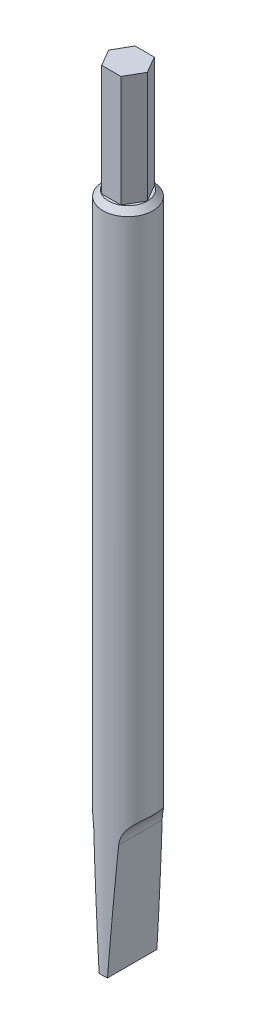
SolidWorks part; units mm, degrees
material "Cast Alloy Steel"
ref_plane "Front Plane" through (0, 0, 0) normal (0, 0, 1) x (1, 0, 0)
ref_plane "Top Plane" through (0, 0, 0) normal (0, 1, 0) x (1, 0, 0)
ref_plane "Right Plane" through (0, 0, 0) normal (1, 0, 0) x (0, 0, -1)
sketch "Sketch1" plane through (0, 0, 0) normal (0, 1, 0) x (1, 0, 0)
  circle A0 centre (0, 0) radius 4.5
  dimension "D1" = 9
extrude "Boss-Extrude1" add sketch "Sketch1" along normal blind 120
sketch "Sketch2" plane through (0, 120, 0) normal (0, 1, 0) x (1, 0, 0)
  line L1 (1.7321, 3) -> (-1.7321, 3)
  line L2 (-1.7321, 3) -> (-3.4641, 0)
  line L3 (-3.4641, 0) -> (-1.7321, -3)
  line L4 (-1.7321, -3) -> (1.7321, -3)
  line L5 (1.7321, -3) -> (3.4641, 0)
  line L6 (3.4641, 0) -> (1.7321, 3)
  circle A0 centre (0, 0) radius 3 construction
  dimension "D1" = 6
extrude "Boss-Extrude2" add sketch "Sketch2" along normal blind 20
chamfer "Chamfer1" distance 1 angle 45 1 edges at (0, 120, 4.5)
sketch "Sketch3" plane through (0, 0, 0) normal (0, 0, 1) x (1, 0, 0)
  line L0 (0.75, 0) -> (2.229, 21.1513)
  line L1 (-4.5, 0) -> (4.5, 0) construction
  line L3 (4.5, 0) -> (4.5, 119) construction
  line L4 (4.5, 25) -> (4.5, 0)
  line L5 (4.5, 0) -> (0.75, 0)
  line L6 (0, 0) -> (0, 10.5792) construction
  line L8 (-4.5, 25) -> (-4.5, 0)
  line L9 (-4.5, 0) -> (-0.75, 0)
  line L10 (-0.75, 0) -> (-2.229, 21.1513)
  arc A0 (2.229, 21.1513) -> (4.5, 25) centre (7.2169, 20.8025) cw
  arc A1 (-2.229, 21.1513) -> (-4.5, 25) centre (-7.2169, 20.8025) ccw
  dimension "D4" = 5
  dimension "D1" = 4
  dimension "D2" = 25
  dimension "D3" = 3.75
extrude "Cut-Extrude1" cut sketch "Sketch3" against normal through all both and the other way through all
